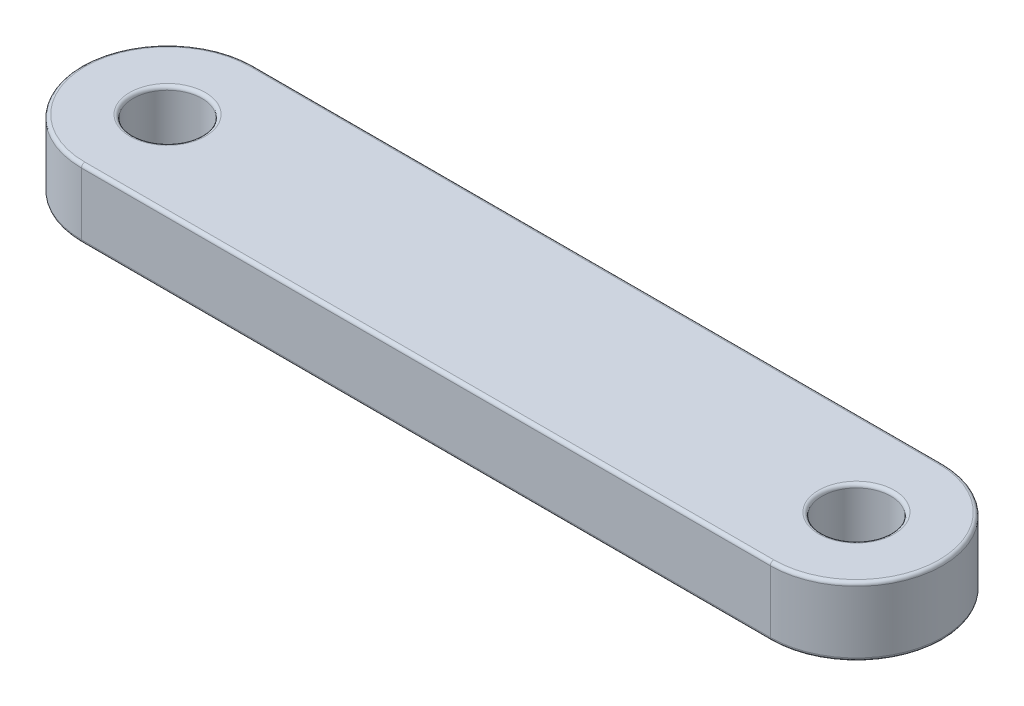
SolidWorks part; units mm, degrees
material "Alloy Steel"
ref_plane "Front Plane" through (0, 0, 0) normal (0, 0, 1) x (1, 0, 0)
ref_plane "Top Plane" through (0, 0, 0) normal (0, 1, 0) x (1, 0, 0)
ref_plane "Right Plane" through (0, 0, 0) normal (1, 0, 0) x (0, 0, -1)
sketch "Sketch1" plane through (0, 0, 0) normal (0, 1, 0) x (1, 0, 0)
  line L0 (-100, 0) -> (100, 0) construction
  line L1 (-100, 25) -> (100, 25)
  line L2 (-100, -25) -> (100, -25)
  line L3 (0, 0) -> (0, 241.5958) construction
  arc A0 (-100, 25) -> (-100, -25) centre (-100, 0) ccw
  arc A1 (100, -25) -> (100, 25) centre (100, 0) ccw
  circle A2 centre (-100, 0) radius 10
  circle A3 centre (100, 0) radius 10
  point P2 (0, 0)
  dimension "D2" = 20
  dimension "D3" = 50
  dimension "D1" = 200
extrude "Boss-Extrude1" add sketch "Sketch1" along normal blind 20
fillet "Fillet1" radius 1 12 edges at (100, 0, -10) (-100, 0, 10) (0, 0, 25) (125, 0, 0) (0, 0, -25) (-125, 0, 0) (100, 20, -10) (0, 20, -25) (125, 20, 0) (0, 20, 25) (-125, 20, 0) (-100, 20, 10)
